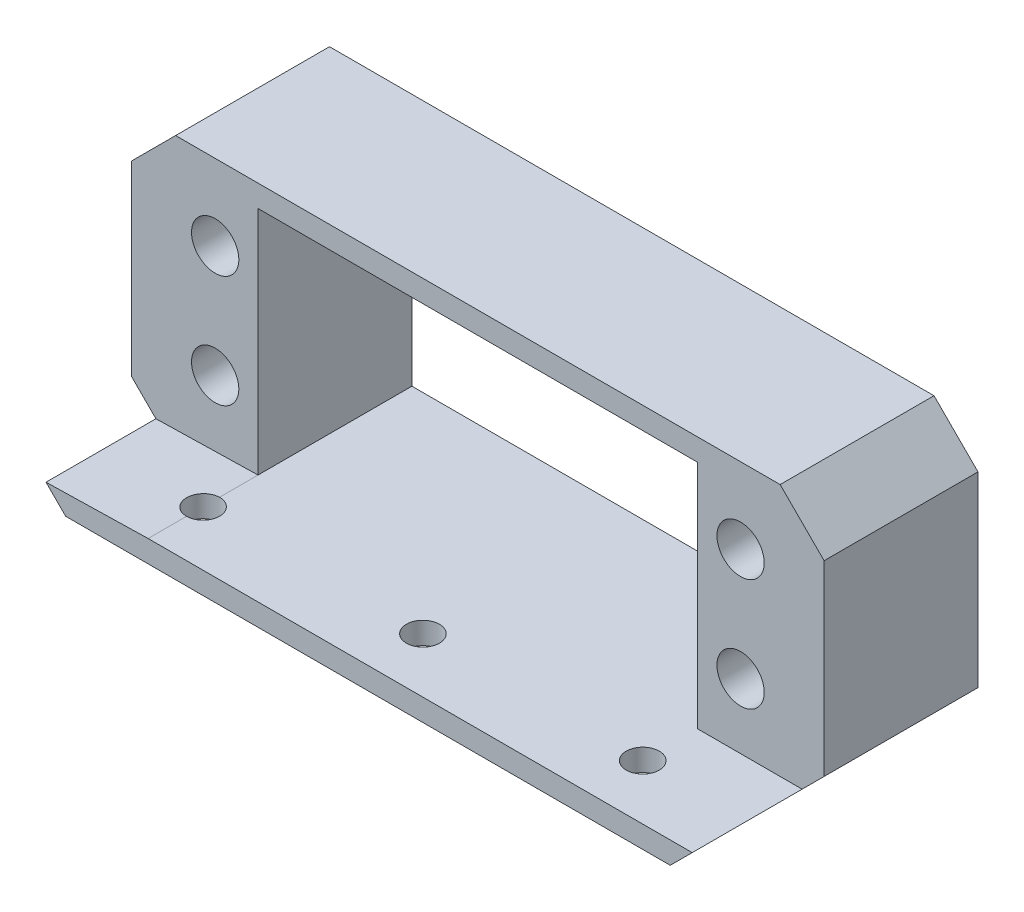
SolidWorks part; units mm, degrees
ref_plane "Front Plane" through (0, 0, 0) normal (0, 0, 1) x (1, 0, 0)
ref_plane "Top Plane" through (0, 0, 0) normal (0, 1, 0) x (1, 0, 0)
ref_plane "Right Plane" through (0, 0, 0) normal (1, 0, 0) x (0, 0, -1)
sketch "Sketch1" plane through (0, 0, 0) normal (0, 0, 1) x (1, 0, 0)
  line L0 (-27.5, 12.5) -> (-31.5, 8.5)
  line L1 (-27.5, 12.5) -> (27.5, 12.5)
  line L2 (-31.5, 8.5) -> (-31.5, -8.5)
  line L3 (-27.5, -12.5) -> (27.5, -12.5)
  line L4 (31.5, 8.5) -> (31.5, -8.5)
  line L5 (-30.6258, 12.1531) -> (28.6364, -11.3636) construction
  line L7 (-20, 10.5) -> (20, 10.5)
  line L8 (-20, 10.5) -> (-20, -10.5)
  line L9 (-20, -10.5) -> (20, -10.5)
  line L10 (20, 10.5) -> (20, -10.5)
  line L11 (-20, 10.5) -> (20, -10.5) construction
  line L12 (-20, -10.5) -> (20, 10.5) construction
  line L13 (0, 0) -> (0, 5.9858) construction
  line L14 (0, 0) -> (6.2989, 0) construction
  line L15 (27.5, 12.5) -> (31.5, 8.5)
  line L16 (27.5, -12.5) -> (31.5, -8.5)
  line L17 (-27.5, -12.5) -> (-31.5, -8.5)
  line L18 (-28.6364, -11.3636) -> (30.6258, 12.1531) construction
  point P0 (0, 0)
  point P6 (0, 0)
  point P26 (-29.5, 10.5)
  dimension "D3" = 40
  dimension "D4" = 21
extrude "Boss-Extrude1" add sketch "Sketch1" along normal blind 14
sketch "Sketch2" plane through (0, 0, 0) normal (0, 0, -1) x (-1, 0, 0)
  circle A0 centre (-23.9, 5.6) radius 2.15
  circle A1 centre (-23.9, -4.6) radius 2.15
  circle A2 centre (23.9, 5.6) radius 2.15
  circle A3 centre (23.9, -4.6) radius 2.15
extrude "Cut-Extrude1" cut sketch "Sketch2" against normal through all
sketch "Sketch3" plane through (0, 0, 14) normal (0, 0, 1) x (1, 0, 0)
  line L0 (-27.5, -12.5) -> (27.5, -12.5) construction
  line L1 (-20, -10.5) -> (20, -10.5) construction
  line L2 (-27.5, -12.5) -> (27.5, -12.5)
  line L3 (-20, -10.5) -> (20, -10.5)
  line L4 (-20, -10.5) -> (-29.2903, -10.7097)
  line L5 (-31.5, -8.5) -> (-27.5, -12.5) construction
  line L6 (-29.2903, -10.7097) -> (-27.5, -12.5)
  line L7 (20, -10.5) -> (29.5, -10.5)
  line L8 (27.5, -12.5) -> (31.5, -8.5) construction
  line L9 (29.5, -10.5) -> (27.5, -12.5)
extrude "Boss-Extrude2" add sketch "Sketch3" along normal blind 10
sketch "Sketch4" plane through (0, -12.5, 0) normal (0, -1, 0) x (1, 0, 0)
  line L0 (-20, 24) -> (-20, 0) construction
  line L1 (0, 24) -> (0, 0) construction
  line L2 (-27.5, 24) -> (27.5, 24) construction
  line L3 (20, 24) -> (20, 0) construction
  circle A0 centre (-20, 19) radius 1.5
  circle A1 centre (20, 19) radius 1.5
  circle A2 centre (0, 19) radius 1.5
  point P15 (-20, 12)
  point P17 (-20, 7.5057)
  dimension "D2" = 3
  dimension "D3" = 5
  dimension "D1" = 2
extrude "Cut-Extrude3" cut sketch "Sketch4" against normal through all
